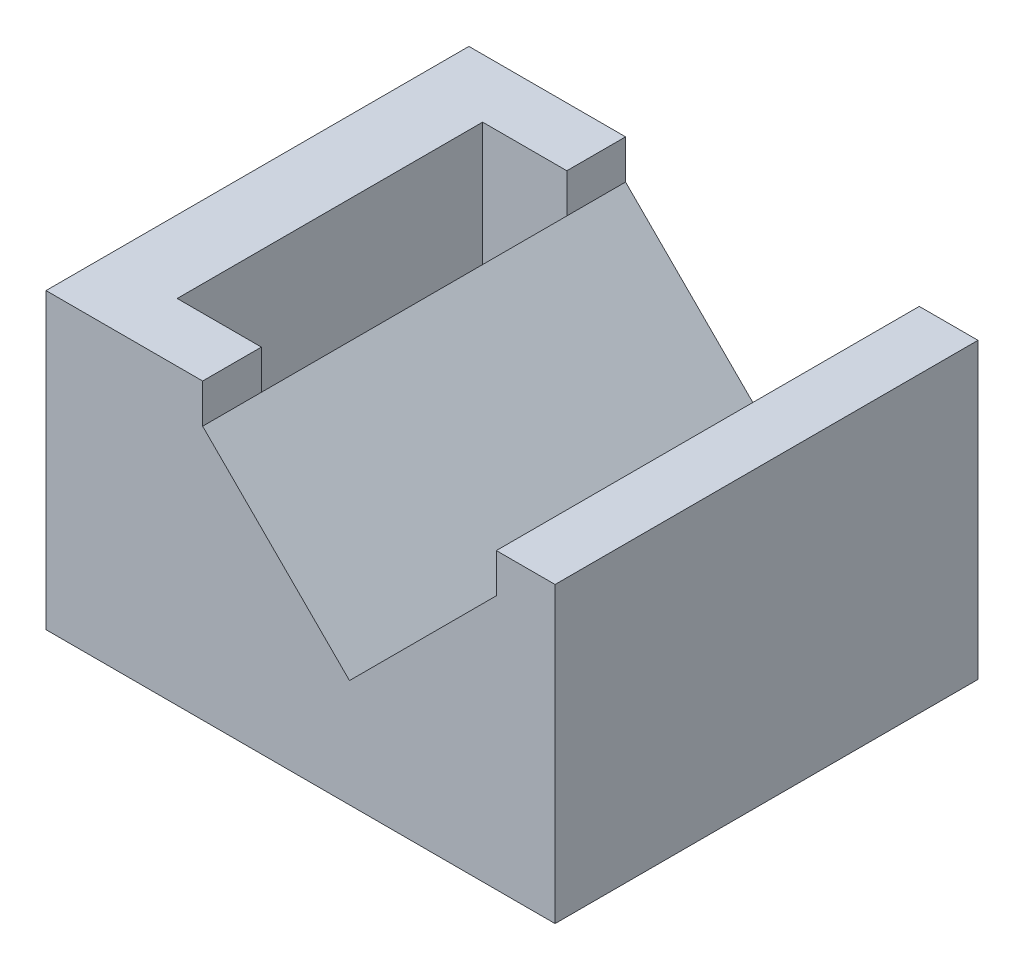
SolidWorks part; units mm, degrees
ref_plane "Plano frontal" through (0, 0, 0) normal (0, 0, 1) x (1, 0, 0)
ref_plane "Plano superior" through (0, 0, 0) normal (0, 1, 0) x (1, 0, 0)
ref_plane "Plano direito" through (0, 0, 0) normal (1, 0, 0) x (0, 0, -1)
sketch "Esboço1" plane through (0, 0, 0) normal (0, 0, 1) x (1, 0, 0)
  line L0 (26, 0) -> (0, 0)
  line L1 (26, 0) -> (26, 15)
  line L2 (23, 13) -> (23, 15)
  line L3 (23, 13) -> (15.5, 5.5)
  line L4 (15.5, 5.5) -> (8, 13)
  line L5 (23, 15) -> (26, 15)
  line L6 (8, 13) -> (8, 15)
  line L7 (8, 15) -> (0, 15)
  line L13 (0, 15) -> (0, 0)
  point P0 (15.7185, 5.2815)
  dimension "D1" = 2
  dimension "D2" = 15
  dimension "D3" = 15
  dimension "D4" = 3
  dimension "D5" = 8
extrude "Ressalto-extrusão1" add sketch "Esboço1" along normal mid plane 50
sketch "Esboço5" plane through (0, 15, 0) normal (0, 1, 0) x (1, 0, 0)
  line L0 (8, -25) -> (8, 25) construction
  line L1 (8, 7.8) -> (3.7, 7.8)
  line L2 (8, 7.8) -> (8, -7.8)
  line L3 (8, -7.8) -> (3.7, -7.8)
  line L4 (3.7, 7.8) -> (3.7, -7.8)
  line L5 (0, -25) -> (0, 25) construction
  line L6 (26, 0) -> (0, 0) construction
  line L7 (0, 25) -> (26, 25)
  line L8 (0, 25) -> (0, 10.8)
  line L9 (0, 10.8) -> (26, 10.8)
  line L10 (26, 25) -> (26, 10.8)
  line L11 (26, -25) -> (26, 25) construction
  line L12 (26, -25) -> (26, -10.8)
  line L13 (0, -10.8) -> (26, -10.8)
  line L14 (0, -25) -> (0, -10.8)
  line L15 (0, -25) -> (26, -25)
  point P6 (3.7, 0)
  point P9 (0, 0)
  point P23 (26, -14.2)
  dimension "D1" = 15.6
  dimension "D2" = 4.3
  dimension "D3" = 3
extrude "Corte-extrusão4" cut sketch "Esboço5" against normal through all both and the other way through all
sketch "Esboço6" plane through (0, 0, 0) normal (0, 0, 1) x (1, 0, 0)
  line L0 (0, 8.5) -> (-3, 4)
  line L1 (0, 0) -> (0, 15) construction
  line L2 (-3, 4) -> (-3, 1)
  line L3 (-3, 1) -> (-2, 1)
  line L4 (-2, 1) -> (0, 4)
  line L5 (26, 0) -> (0, 0) construction
  line L6 (0, 8.5) -> (0, 4)
  dimension "D1" = 3
  dimension "D2" = 1
  dimension "D3" = 3
  dimension "D4" = 1
extrude "Ressalto-extrusão2" add sketch "Esboço6" along normal mid plane 5
